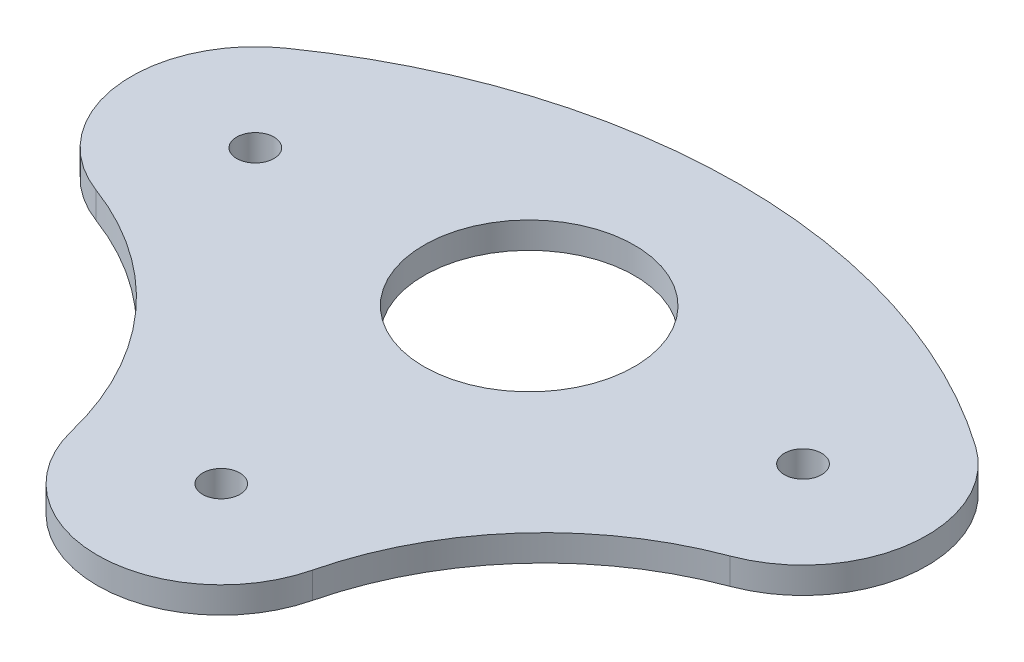
SolidWorks part; units mm, degrees
ref_plane "Front Plane" through (0, 0, 0) normal (0, 0, 1) x (1, 0, 0)
ref_plane "Top Plane" through (0, 0, 0) normal (0, 1, 0) x (1, 0, 0)
ref_plane "Right Plane" through (0, 0, 0) normal (1, 0, 0) x (0, 0, -1)
sketch "Sketch1" plane through (0, 0, 0) normal (0, 1, 0) x (1, 0, 0)
  line L0 (30.7848, 0) -> (-30.7848, 0) construction
  line L1 (31.5396, -1.6814) -> (1.4952, -35.4668) construction
  circle A0 centre (0, 0) radius 12.7
  circle A1 centre (-33.0348, 0) radius 2.25
  circle A2 centre (33.0348, 0) radius 2.25
  circle A3 centre (0, -37.1481) radius 2.25
  arc A5 (-41.6328, 12.2302) -> (-38.2495, -14.011) centre (-33.0348, 0) ccw
  arc A6 (-14.5243, -40.6905) -> (14.5243, -40.6905) centre (0, -37.1481) ccw
  arc A7 (38.2495, -14.011) -> (41.6328, 12.2302) centre (33.0348, 0) ccw
  arc A8 (-38.2495, -14.011) -> (-14.5243, -40.6905) centre (-51.5393, -49.7181) cw
  arc A9 (14.5243, -40.6905) -> (38.2495, -14.011) centre (51.5393, -49.7181) cw
  arc A10 (-41.6328, 12.2302) -> (41.6328, 12.2302) centre (0, -46.9902) cw
  point P2 (0, 25.4)
  point P20 (0, -32.9096)
  point P21 (-37.1002, -14.95)
  point P22 (0, 0)
  point P23 (0, 12.7)
  point P24 (38.4929, -13.918)
  dimension "D1" = 4.5
  dimension "D2" = 25.4
  dimension "D4" = 12.7
  dimension "D5" = 12.7
  dimension "D3" = 61.5696
  dimension "D6" = 45.212
  dimension "D7" = 38.1
extrude "Boss-Extrude1" add sketch "Sketch1" along normal blind 3.175
